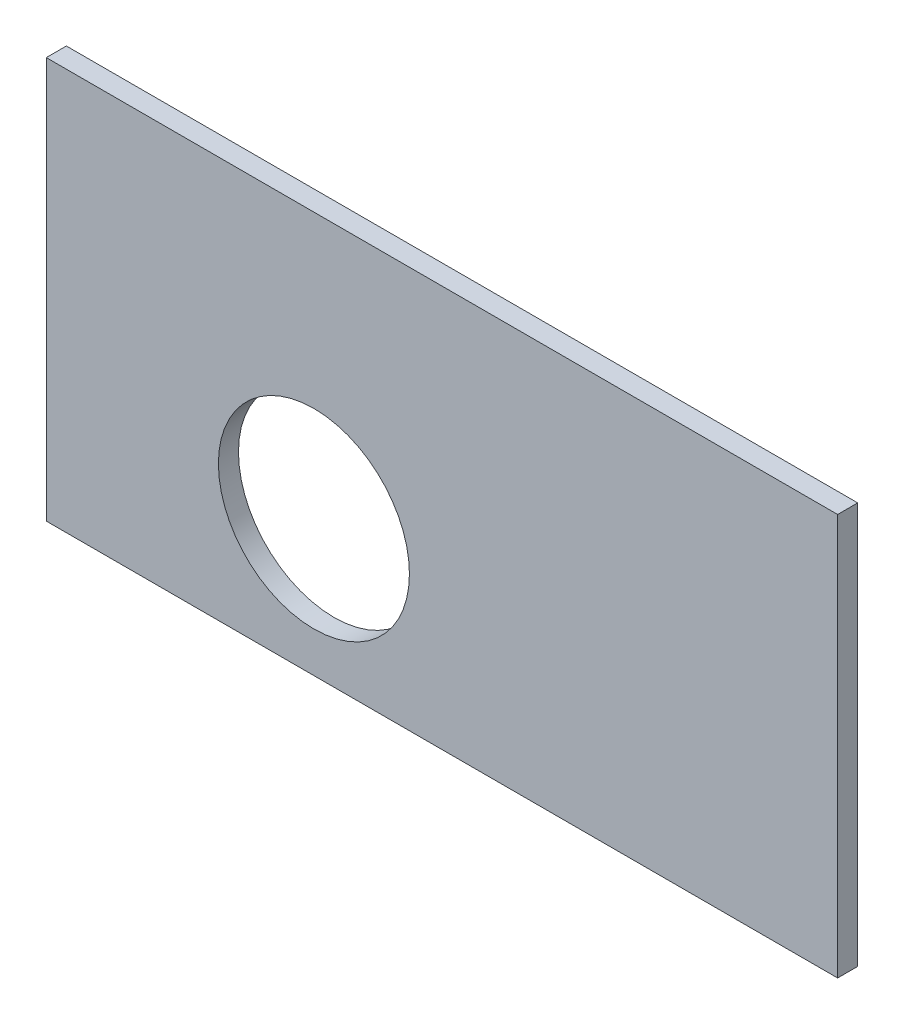
SolidWorks part; units mm, degrees
ref_plane "Front Plane" through (0, 0, 0) normal (0, 0, 1) x (1, 0, 0)
ref_plane "Top Plane" through (0, 0, 0) normal (0, 1, 0) x (1, 0, 0)
ref_plane "Right Plane" through (0, 0, 0) normal (1, 0, 0) x (0, 0, -1)
sketch "Sketch1" plane through (0, 0, 0) normal (0, 0, 1) x (1, 0, 0)
  line L1 (0, 0) -> (118.28, 0)
  line L2 (0, 0) -> (0, 60)
  line L3 (0, 60) -> (118.28, 60)
  line L4 (118.28, 0) -> (118.28, 60)
  dimension "D1" = 118.28
  dimension "D2" = 60
extrude "Boss-Extrude1" add sketch "Sketch1" along normal blind 3
sketch "Sketch2" plane through (0, 0, 3) normal (0, 0, 1) x (1, 0, 0)
  line L0 (118.28, 60) -> (0, 60) construction
  line L2 (0, 60) -> (0, 0) construction
  circle A0 centre (40, 20.31) radius 14.275
  dimension "D1" = 28.55
  dimension "D2" = 40
  dimension "D3" = 39.69
extrude "Cut-Extrude1" cut sketch "Sketch2" against normal blind 3
